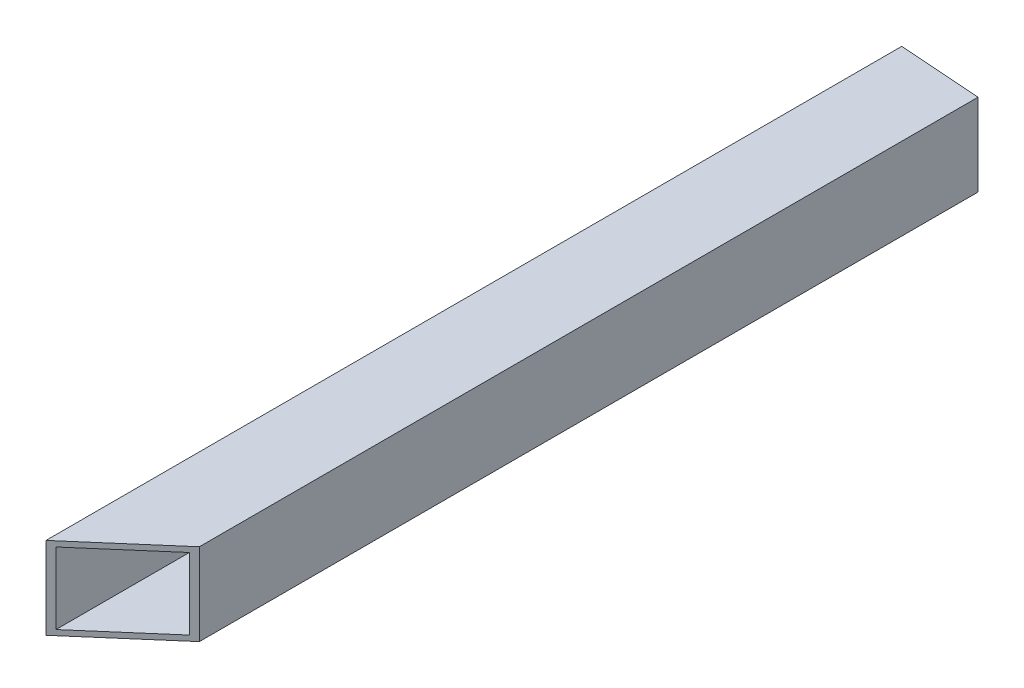
SolidWorks part; units mm, degrees
ref_plane "Front Plane" through (0, 0, 0) normal (0, 0, 1) x (1, 0, 0)
ref_plane "Top Plane" through (0, 0, 0) normal (0, 1, 0) x (1, 0, 0)
ref_plane "Right Plane" through (0, 0, 0) normal (1, 0, 0) x (0, 0, -1)
sketch "Sketch1" plane through (0, 0, 0) normal (0, 0, 1) x (1, 0, 0)
  line L1 (11.049, 11.049) -> (-11.049, 11.049)
  line L2 (11.049, 11.049) -> (11.049, -11.049)
  line L3 (11.049, -11.049) -> (-11.049, -11.049)
  line L4 (-11.049, 11.049) -> (-11.049, -11.049)
  line L5 (11.049, 11.049) -> (-11.049, -11.049) construction
  line L6 (11.049, -11.049) -> (-11.049, 11.049) construction
  line L7 (12.7, 12.7) -> (-12.7, 12.7)
  line L8 (12.7, 12.7) -> (12.7, -12.7)
  line L9 (12.7, -12.7) -> (-12.7, -12.7)
  line L10 (-12.7, 12.7) -> (-12.7, -12.7)
  line L11 (12.7, 12.7) -> (-12.7, -12.7) construction
  line L12 (12.7, -12.7) -> (-12.7, 12.7) construction
  point P0 (0, 0)
  point P6 (0, 0)
  dimension "D3" = 1.651
  dimension "D4" = 1.651
  dimension "D5" = 1.651
  dimension "D2" = 25.4
  dimension "D1" = 25.4
extrude "Boss-Extrude1" add sketch "Sketch1" along normal up to vertex (252.579 mm away)
sketch "Sketch3" plane through (0, 0, 0) normal (0, 1, 0) x (1, 0, 0)
  line L0 (0, 12.8662) -> (0, -262.1311) construction
  line L1 (0, -13.97) -> (0, 13.97) construction
ref_point "Point1"
sketch "Sketch5" plane through (0, 0, 252.579) normal (0, 0, 1) x (1, 0, 0)
  line L0 (12.7, -12.7) -> (12.7, 12.7) construction
  line L1 (11.049, -11.049) -> (11.049, 11.049) construction
  line L2 (12.7, 12.7) -> (-12.7, 12.7) construction
  line L3 (11.049, 11.049) -> (-11.049, 11.049) construction
  line L4 (-11.049, 11.049) -> (-11.049, -11.049) construction
  line L5 (-12.7, 12.7) -> (-12.7, -12.7) construction
  line L6 (-12.7, -12.7) -> (12.7, -12.7) construction
  line L7 (-11.049, -11.049) -> (11.049, -11.049) construction
  line L8 (12.7, -12.7) -> (12.7, 12.7)
  line L9 (11.049, -11.049) -> (11.049, 11.049)
  line L10 (12.7, 12.7) -> (-12.7, 12.7)
  line L11 (11.049, 11.049) -> (-11.049, 11.049)
  line L12 (-11.049, 11.049) -> (-11.049, -11.049)
  line L13 (-12.7, 12.7) -> (-12.7, -12.7)
  line L14 (-12.7, -12.7) -> (12.7, -12.7)
  line L15 (-11.049, -11.049) -> (11.049, -11.049)
extrude "Boss-Extrude2" add sketch "Sketch5" along normal blind 12.7
sketch "Sketch6" plane through (0, -22.7, 252.579) normal (0, -1, 0) x (-0.1425, 0, 0.9898)
  line L0 (-25.0493, -21.7022) -> (26.8699, 23.2796)
  line L2 (-12.7371, -11.0352) -> (-29.694, 4.2737) construction
  line L3 (-262.7379, 37.8143) -> (9.4547, -1.3608) construction
  line L4 (-12.7371, -11.0352) -> (0, -30) construction
  line L5 (0, 12.8662) -> (0, -262.1311) construction
  line L6 (-25.0493, -21.7022) -> (45.865, -41.5515)
  line L7 (45.865, -41.5515) -> (26.8699, 23.2796)
  dimension "D1" = 30
  dimension "D2" = 30
extrude "Cut-Extrude1" cut sketch "Sketch6" against normal through all
sketch "Sketch7" plane through (0, 0, 0) normal (0, 0, -1) x (-1, 0, 0)
  line L0 (12.7, -12.7) -> (-12.7, -12.7) construction
  line L1 (-12.7, -12.7) -> (-12.7, 12.7) construction
  line L2 (12.7, 12.7) -> (12.7, -12.7) construction
  line L3 (-12.7, 12.7) -> (12.7, 12.7) construction
  line L4 (-11.049, -11.049) -> (-11.049, 11.049) construction
  line L5 (-11.049, 11.049) -> (11.049, 11.049) construction
  line L6 (11.049, 11.049) -> (11.049, -11.049) construction
  line L7 (11.049, -11.049) -> (-11.049, -11.049) construction
  line L8 (12.7, -12.7) -> (-12.7, -12.7)
  line L9 (-12.7, -12.7) -> (-12.7, 12.7)
  line L10 (12.7, 12.7) -> (12.7, -12.7)
  line L11 (-12.7, 12.7) -> (12.7, 12.7)
  line L12 (-11.049, -11.049) -> (-11.049, 11.049)
  line L13 (-11.049, 11.049) -> (11.049, 11.049)
  line L14 (11.049, 11.049) -> (11.049, -11.049)
  line L15 (11.049, -11.049) -> (-11.049, -11.049)
extrude "Boss-Extrude3" add sketch "Sketch7" along normal blind 25.4
sketch "Sketch8" plane through (602.972, 151.3216, -52.6684) normal (0, -1, 0) x (0.1425, 0, -0.9898)
  line L0 (-136.2089, -563.9061) -> (-139.8477, -614.7326)
  line L1 (-152.8753, -587.1825) -> (-136.2089, -563.9061) construction
  line L2 (-125.2934, -591.1522) -> (-397.4859, -551.9772) construction
  line L3 (-136.2089, -563.9061) -> (-123.0283, -589.3194) construction
  line L4 (124.8378, -589.3194) -> (-150.1594, -589.3194) construction
  line L5 (-139.8477, -614.7326) -> (-41.7256, -599.2804)
  line L6 (-41.7256, -599.2804) -> (-136.2089, -563.9061)
  line L7 (-136.2089, -372.0194) -> (-136.2089, -576.6194) construction
  point P3 (-136.2089, -561.4685)
  point P13 (-136.2089, -563.9061)
  point P14 (0, 0)
  point P15 (-136.2089, -563.9061)
  point P16 (-139.8477, -614.7326)
  point P17 (-139.8477, -614.7326)
  point P18 (-136.2089, -563.9061)
  point P19 (-136.2089, -563.9061)
  point P20 (-136.2089, -563.9061)
  point P21 (0, 0)
  point P22 (-41.7256, -599.2804)
  point P23 (-139.8477, -614.7326)
  dimension "D1" = 15
  dimension "D2" = 15
extrude "Cut-Extrude2" cut sketch "Sketch8" along normal through all
equation "\"c1c2Len\"= 250"
equation "\"D1\"= \"c1c2Len\""
equation "\"1inchSquareTubeLen\"=25.4"
equation "\"D2@Sketch1\"=\"1inchSquareTubeLen\""
equation "\"D1@Sketch1\"=\"1inchSquareTubeLen\""
equation "\"squareTubeWallThickness\"=1.651"
equation "\"D5@Sketch1\"=\"squareTubeWallThickness\""
equation "\"D4@Sketch1\"=\"squareTubeWallThickness\""
equation "\"D3@Sketch1\"=\"squareTubeWallThickness\""
